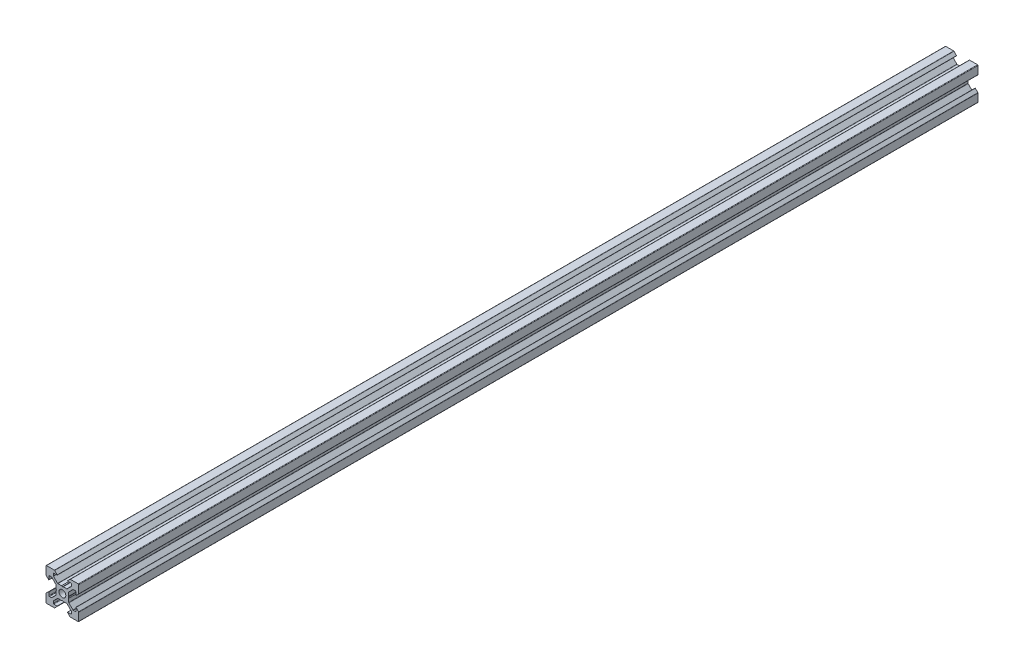
SolidWorks part; units mm, degrees
material "6063-T5"
ref_plane "Plan de face" through (0, 0, 0) normal (0, 0, 1) x (1, 0, 0)
ref_plane "Plan de dessus" through (0, 0, 0) normal (0, 1, 0) x (1, 0, 0)
ref_plane "Plan de droite" through (0, 0, 0) normal (1, 0, 0) x (0, 0, -1)
sketch "Esquisse1" plane through (0, 0, 0) normal (0, 0, 1) x (1, 0, 0)
  line L0 (18.7749, -2.8952) -> (18.7749, -4.8946)
  line L1 (18.4749, -5.1946) -> (17.2591, -5.1946)
  line L2 (17.047, -5.1067) -> (14.5634, -2.6231)
  line L3 (14.4755, -2.411) -> (14.4755, -0.2148)
  line L4 (14.4755, -0.2148) -> (14.1755, 0.3048)
  line L5 (14.1755, 0.3048) -> (14.4755, 0.8244)
  line L6 (14.4755, 0.8244) -> (14.4755, 3.0205)
  line L7 (14.5634, 3.2326) -> (17.047, 5.7162)
  line L8 (17.2591, 5.8041) -> (18.4749, 5.8041)
  line L9 (18.7749, 5.5041) -> (18.7749, 3.5048)
  line L10 (18.9456, 3.4341) -> (20.487, 4.9755)
  line L11 (20.5749, 5.1876) -> (20.5749, 10.0048)
  line L12 (20.2749, 10.3048) -> (15.4577, 10.3048)
  line L13 (15.2456, 10.2169) -> (13.7041, 8.6755)
  line L14 (13.7749, 8.5048) -> (15.7742, 8.5048)
  line L15 (16.0742, 8.2048) -> (16.0742, 6.989)
  line L16 (15.9863, 6.7769) -> (13.5027, 4.2933)
  line L17 (13.2906, 4.2054) -> (11.0945, 4.2054)
  line L18 (11.0945, 4.2054) -> (10.5749, 3.9054)
  line L19 (10.5749, 3.9054) -> (10.0552, 4.2054)
  line L20 (10.0552, 4.2054) -> (7.8591, 4.2054)
  line L21 (7.647, 4.2933) -> (5.1634, 6.7769)
  line L22 (5.0755, 6.989) -> (5.0755, 8.2048)
  line L23 (5.3755, 8.5048) -> (7.3749, 8.5048)
  line L24 (7.4456, 8.6755) -> (5.9041, 10.2169)
  line L25 (5.692, 10.3048) -> (0.8749, 10.3048)
  line L26 (0.5749, 10.0048) -> (0.5749, 5.1876)
  line L27 (0.6627, 4.9755) -> (2.2041, 3.4341)
  line L28 (2.3749, 3.5048) -> (2.3749, 5.5041)
  line L29 (2.6749, 5.8041) -> (3.8906, 5.8041)
  line L30 (4.1027, 5.7162) -> (6.5863, 3.2326)
  line L31 (6.6742, 3.0205) -> (6.6742, 0.8244)
  line L32 (6.6742, 0.8244) -> (6.9742, 0.3048)
  line L33 (6.9742, 0.3048) -> (6.6742, -0.2148)
  line L34 (6.6742, -0.2148) -> (6.6742, -2.411)
  line L35 (6.5863, -2.6231) -> (4.1027, -5.1067)
  line L36 (3.8906, -5.1946) -> (2.6749, -5.1946)
  line L37 (2.3749, -4.8946) -> (2.3749, -2.8952)
  line L38 (2.2041, -2.8245) -> (0.6627, -4.3659)
  line L39 (0.5749, -4.5781) -> (0.5749, -9.3952)
  line L40 (0.8749, -9.6952) -> (5.692, -9.6952)
  line L41 (5.9041, -9.6074) -> (7.4456, -8.0659)
  line L42 (7.3749, -7.8952) -> (5.3755, -7.8952)
  line L43 (5.0755, -7.5952) -> (5.0755, -6.3795)
  line L44 (5.1634, -6.1674) -> (7.647, -3.6838)
  line L45 (7.8591, -3.5959) -> (10.0552, -3.5959)
  line L46 (10.0552, -3.5959) -> (10.5749, -3.2959)
  line L47 (10.5749, -3.2959) -> (11.0945, -3.5959)
  line L48 (11.0945, -3.5959) -> (13.2906, -3.5959)
  line L49 (13.5027, -3.6838) -> (15.9863, -6.1674)
  line L50 (16.0742, -6.3795) -> (16.0742, -7.5952)
  line L51 (15.7742, -7.8952) -> (13.7749, -7.8952)
  line L52 (13.7041, -8.0659) -> (15.2456, -9.6074)
  line L53 (15.4577, -9.6952) -> (20.2749, -9.6952)
  line L54 (20.5749, -9.3952) -> (20.5749, -4.5781)
  line L55 (20.487, -4.3659) -> (18.9456, -2.8245)
  arc A0 (10.5749, -1.7952) -> (12.6749, 0.3048) centre (10.5749, 0.3048) ccw
  arc A1 (12.6749, 0.3048) -> (10.5749, 2.4048) centre (10.5749, 0.3048) ccw
  arc A2 (10.5749, 2.4048) -> (8.4749, 0.3048) centre (10.5749, 0.3048) ccw
  arc A3 (8.4749, 0.3048) -> (10.5749, -1.7952) centre (10.5749, 0.3048) ccw
  arc A4 (18.9456, -2.8245) -> (18.7749, -2.8952) centre (18.8749, -2.8952) ccw
  arc A5 (18.4749, -5.1946) -> (18.7749, -4.8946) centre (18.4749, -4.8946) ccw
  arc A6 (17.047, -5.1067) -> (17.2591, -5.1946) centre (17.2591, -4.8946) ccw
  arc A7 (14.4755, -2.411) -> (14.5634, -2.6231) centre (14.7755, -2.411) ccw
  arc A8 (14.5634, 3.2326) -> (14.4755, 3.0205) centre (14.7755, 3.0205) ccw
  arc A9 (17.2591, 5.8041) -> (17.047, 5.7162) centre (17.2591, 5.5041) ccw
  arc A10 (18.7749, 5.5041) -> (18.4749, 5.8041) centre (18.4749, 5.5041) ccw
  arc A11 (18.7749, 3.5048) -> (18.9456, 3.4341) centre (18.8749, 3.5048) ccw
  arc A12 (20.487, 4.9755) -> (20.5749, 5.1876) centre (20.2749, 5.1876) ccw
  arc A13 (20.5749, 10.0048) -> (20.2749, 10.3048) centre (20.2749, 10.0048) ccw
  arc A14 (15.4577, 10.3048) -> (15.2456, 10.2169) centre (15.4577, 10.0048) ccw
  arc A15 (13.7041, 8.6755) -> (13.7749, 8.5048) centre (13.7749, 8.6048) ccw
  arc A16 (16.0742, 8.2048) -> (15.7742, 8.5048) centre (15.7742, 8.2048) ccw
  arc A17 (15.9863, 6.7769) -> (16.0742, 6.989) centre (15.7742, 6.989) ccw
  arc A18 (13.2906, 4.2054) -> (13.5027, 4.2933) centre (13.2906, 4.5054) ccw
  arc A19 (7.647, 4.2933) -> (7.8591, 4.2054) centre (7.8591, 4.5054) ccw
  arc A20 (5.0755, 6.989) -> (5.1634, 6.7769) centre (5.3755, 6.989) ccw
  arc A21 (5.3755, 8.5048) -> (5.0755, 8.2048) centre (5.3755, 8.2048) ccw
  arc A22 (7.3749, 8.5048) -> (7.4456, 8.6755) centre (7.3749, 8.6048) ccw
  arc A23 (5.9041, 10.2169) -> (5.692, 10.3048) centre (5.692, 10.0048) ccw
  arc A24 (0.8749, 10.3048) -> (0.5749, 10.0048) centre (0.8749, 10.0048) ccw
  arc A25 (0.5749, 5.1876) -> (0.6627, 4.9755) centre (0.8749, 5.1876) ccw
  arc A26 (2.2041, 3.4341) -> (2.3749, 3.5048) centre (2.2749, 3.5048) ccw
  arc A27 (2.6749, 5.8041) -> (2.3749, 5.5041) centre (2.6749, 5.5041) ccw
  arc A28 (4.1027, 5.7162) -> (3.8906, 5.8041) centre (3.8906, 5.5041) ccw
  arc A29 (6.6742, 3.0205) -> (6.5863, 3.2326) centre (6.3742, 3.0205) ccw
  arc A30 (6.5863, -2.6231) -> (6.6742, -2.411) centre (6.3742, -2.411) ccw
  arc A31 (3.8906, -5.1946) -> (4.1027, -5.1067) centre (3.8906, -4.8946) ccw
  arc A32 (2.3749, -4.8946) -> (2.6749, -5.1946) centre (2.6749, -4.8946) ccw
  arc A33 (2.3749, -2.8952) -> (2.2041, -2.8245) centre (2.2749, -2.8952) ccw
  arc A34 (0.6627, -4.3659) -> (0.5749, -4.5781) centre (0.8749, -4.5781) ccw
  arc A35 (0.5749, -9.3952) -> (0.8749, -9.6952) centre (0.8749, -9.3952) ccw
  arc A36 (5.692, -9.6952) -> (5.9041, -9.6074) centre (5.692, -9.3952) ccw
  arc A37 (7.4456, -8.0659) -> (7.3749, -7.8952) centre (7.3749, -7.9952) ccw
  arc A38 (5.0755, -7.5952) -> (5.3755, -7.8952) centre (5.3755, -7.5952) ccw
  arc A39 (5.1634, -6.1674) -> (5.0755, -6.3795) centre (5.3755, -6.3795) ccw
  arc A40 (7.8591, -3.5959) -> (7.647, -3.6838) centre (7.8591, -3.8959) ccw
  arc A41 (13.5027, -3.6838) -> (13.2906, -3.5959) centre (13.2906, -3.8959) ccw
  arc A42 (16.0742, -6.3795) -> (15.9863, -6.1674) centre (15.7742, -6.3795) ccw
  arc A43 (15.7742, -7.8952) -> (16.0742, -7.5952) centre (15.7742, -7.5952) ccw
  arc A44 (13.7749, -7.8952) -> (13.7041, -8.0659) centre (13.7749, -7.9952) ccw
  arc A45 (15.2456, -9.6074) -> (15.4577, -9.6952) centre (15.4577, -9.3952) ccw
  arc A46 (20.2749, -9.6952) -> (20.5749, -9.3952) centre (20.2749, -9.3952) ccw
  arc A47 (20.5749, -4.5781) -> (20.487, -4.3659) centre (20.2749, -4.5781) ccw
extrude "Boss.-Extru.1" add sketch "Esquisse1" along normal blind 550
